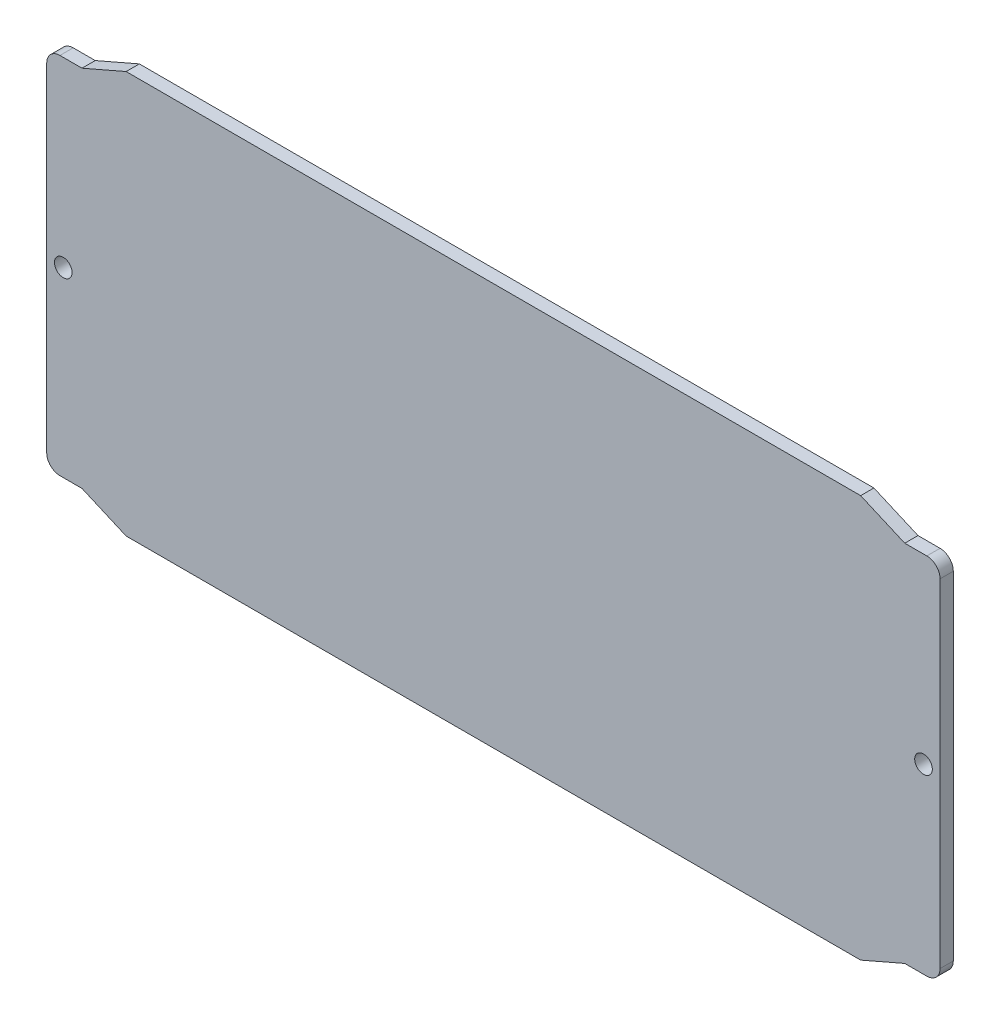
SolidWorks part; units mm, degrees
material "Acrylic (Medium-high impact)"
ref_plane "Front Plane" through (0, 0, 0) normal (0, 0, 1) x (1, 0, 0)
ref_plane "Top Plane" through (0, 0, 0) normal (0, 1, 0) x (1, 0, 0)
ref_plane "Right Plane" through (0, 0, 0) normal (1, 0, 0) x (0, 0, -1)
sketch "Sketch1" plane through (0, 0, 0) normal (0, 0, 1) x (1, 0, 0)
  line L0 (0, 7.34) -> (0, 83.84)
  line L1 (3, 86.84) -> (8, 86.84)
  line L2 (8, 86.84) -> (18, 91.18)
  line L3 (18, 91.18) -> (184.5, 91.18)
  line L4 (184.5, 91.18) -> (194.5, 86.84)
  line L5 (194.5, 86.84) -> (199.5, 86.84)
  line L6 (202.5, 83.84) -> (202.5, 7.34)
  line L7 (199.5, 4.34) -> (194.5, 4.34)
  line L8 (194.5, 4.34) -> (184.5, 0)
  line L9 (184.5, 0) -> (18, 0)
  line L10 (18, 0) -> (8, 4.34)
  line L11 (8, 4.34) -> (3, 4.34)
  arc A0 (0, 83.84) -> (3, 86.84) centre (3, 83.84) cw
  arc A1 (199.5, 86.84) -> (202.5, 83.84) centre (199.5, 83.84) cw
  arc A2 (202.5, 7.34) -> (199.5, 4.34) centre (199.5, 7.34) cw
  arc A3 (3, 4.34) -> (0, 7.34) centre (3, 7.34) cw
  dimension "D2" = 3
  dimension "D1" = 202.5
  dimension "D3" = 8
  dimension "D4" = 4.34
  dimension "D5" = 10
  dimension "D6" = 91.18
extrude "Boss-Extrude1" add sketch "Sketch1" along normal blind 3
hole_wizard "Ø4.0mm Dowel Hole1" positions "Sketch7" profile "Sketch8" hole size "Ø4.0" standard "ANSI Metric" end condition through all
sketch "Sketch7" plane through (0, 0, 3) normal (0, 0, 1) x (1, 0, 0)
  line L0 (3.75, 45.59) -> (198.75, 45.59) construction
  line L2 (184.5, 91.18) -> (18, 91.18) construction
  line L3 (202.5, 7.34) -> (202.5, 83.84) construction
  point P0 (3.75, 45.59)
  point P2 (198.75, 45.59)
  point P12 (101.25, 91.18)
  point P13 (101.25, 45.59)
  point P16 (202.5, 45.59)
  dimension "D1" = 3.75
sketch "Sketch8" plane through (3.75, 45.59, 3) normal (1, 0, 0) x (0, -1, 0)
  line L0 (0, 0) -> (0, 3)
  line L1 (0, 3) -> (2, 3)
  line L2 (2, 3) -> (2, 0)
  line L5 (2, 0) -> (0, 0)
  line L11 (0, -6.35) -> (0, 107.95) construction
  dimension "Thru Hole Dia." = 4
  dimension "Thru Hole Depth" = 3
sketch "Sketch6" [suppressed] plane through (0, 0, 0) normal (0, 0, -1) x (-1, 0, 0)
  line L0 (-184.5, 91.18) -> (-18, 91.18) construction
  line L1 (-30, 81.18) -> (-172.5, 81.18) construction
  line L2 (-30, 81.18) -> (-30, 10) construction
  line L3 (-30, 10) -> (-172.5, 10) construction
  line L4 (-172.5, 81.18) -> (-172.5, 10) construction
  line L5 (-202.5, 7.34) -> (-202.5, 83.84) construction
  line L7 (-95.7652, 45.59) -> (-103.9924, 40.84) construction
  line L8 (-95.7652, 45.59) -> (-98.5076, 50.34)
  line L9 (-98.5076, 50.34) -> (-103.9924, 50.34)
  line L10 (-103.9924, 50.34) -> (-106.7348, 45.59)
  line L11 (-106.7348, 45.59) -> (-103.9924, 40.84)
  line L12 (-103.9924, 40.84) -> (-98.5076, 40.84)
  line L13 (-98.5076, 40.84) -> (-95.7652, 45.59)
  circle A0 centre (-101.25, 45.59) radius 4.75 construction
  point P6 (-101.25, 91.18)
  point P7 (-101.25, 81.18)
  point P10 (-202.5, 45.59)
  point P11 (-172.5, 45.59)
  point P21 (-30, 45.59)
  dimension "D1" = 30
  dimension "D2" = 10
  dimension "D3" = 9.5
extrude "Cut-Extrude1" [suppressed] cut sketch "Sketch6" against normal up to next
fillet "Fillet1" [suppressed] radius 3
pattern_linear "LPattern1" [suppressed] count 7 spacing 13 along (0, -1, 0) count 7 spacing 13 along (0.866, -0.5, 0)
ref_plane "Plane1" [suppressed] through (101.25, 0, 0) normal (1, 0, 0) x (0, 0, -1)
ref_plane "Plane2" [suppressed] through (0, 45.59, 0) normal (0, 1, 0) x (1, 0, 0)
mirror "Mirror2" [suppressed] about plane through (0, 45.59, 0) normal (0, 1, 0)
sketch "Sketch9" [suppressed] plane through (0, 0, 0) normal (0, 0, -1) x (-1, 0, 0)
  line L1 (-38, 76.45) -> (-114.6, 14.73) construction
  line L3 (-114.6, 76.45) -> (-38, 14.73) construction
  line L5 (0, 83.84) -> (0, 7.34) construction
  point P0 (-38, 76.45)
  point P2 (-38, 14.73)
  point P4 (-114.6, 14.73)
  point P6 (-114.6, 76.45)
  point P26 (0, 45.59)
  point P27 (-76.3, 45.59)
  dimension "D1" = 20
  dimension "D2" = 76.6
  dimension "D3" = 61.72
sketch "Sketch12" [suppressed] plane through (0, 0, 0) normal (0, 0, -1) x (-1, 0, 0)
  point P0 (-114.6, 76.45)
  point P3 (-38, 76.45)
  point P6 (-38, 14.73)
  point P9 (-114.6, 14.73)
hole_wizard "Ø3.0mm Dowel Hole2" [suppressed] positions "Sketch12" profile "Sketch13" hole size "Ø3.0" standard "ANSI Metric"
sketch "Sketch13" [suppressed] plane through (114.6, 76.45, 0) normal (1, 0, 0) x (0, 1, 0)
  line L0 (0, 0) -> (0, 3)
  line L1 (0, 3) -> (1.75, 3)
  line L2 (1.75, 3) -> (1.75, 0)
  line L5 (1.75, 0) -> (0, 0)
  line L11 (0, -6.35) -> (0, 107.95) construction
  dimension "Thru Hole Dia." = 3.5
  dimension "Thru Hole Depth" = 3
equation "\"beamDepth\"= 187mm"
equation "\"D1@Sketch1\"=15.5 + \"beamDepth\""
